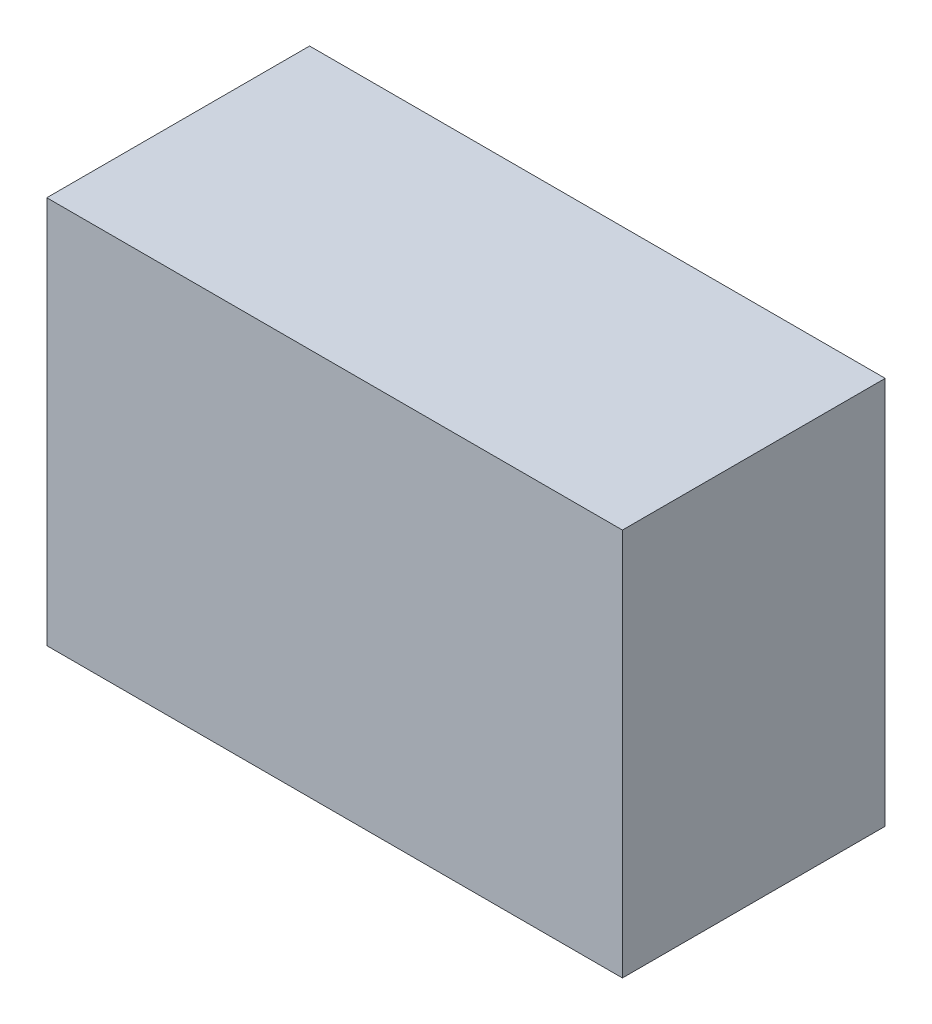
SolidWorks part; units mm, degrees
ref_plane "正面" through (0, 0, 0) normal (0, 0, 1) x (1, 0, 0)
ref_plane "平面" through (0, 0, 0) normal (0, 1, 0) x (1, 0, 0)
ref_plane "右側面" through (0, 0, 0) normal (1, 0, 0) x (0, 0, -1)
sketch "ｽｹｯﾁ1" plane through (0, 0, 0) normal (0, 0, 1) x (1, 0, 0)
  line L1 (0, 0) -> (46, 0)
  line L2 (0, 0) -> (0, 31)
  line L3 (0, 31) -> (46, 31)
  line L4 (46, 0) -> (46, 31)
  dimension "D1" = 46
  dimension "D2" = 31
extrude "ﾎﾞｽ - 押し出し1" add sketch "ｽｹｯﾁ1" along normal blind 21
sketch "ｽｹｯﾁ2" plane through (0, 0, 0) normal (0, -1, 0) x (1, 0, 0)
  line L0 (0, 10.5) -> (-1, 10.5) construction
  line L1 (0, 21) -> (0, 0) construction
  circle A0 centre (-1, 11.5) radius 1
  circle A1 centre (-1, 9.5) radius 1
  dimension "D1" = 2
extrude "ﾎﾞｽ - 押し出し2" add sketch "ｽｹｯﾁ2" along normal blind 5 and the other way blind 5 separate body contours A0 | A1
